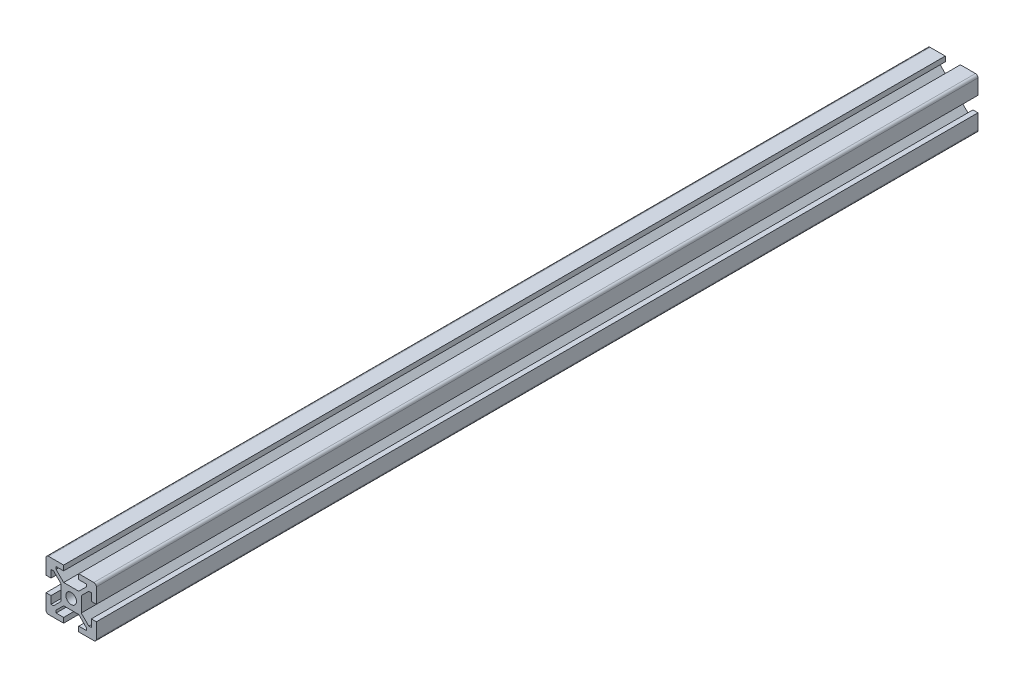
SolidWorks part; units mm, degrees
material "6063-O, Barra estrusa (SS)"
ref_plane "Piano frontale" through (0, 0, 0) normal (0, 0, 1) x (1, 0, 0)
ref_plane "Piano superiore" through (0, 0, 0) normal (0, 1, 0) x (1, 0, 0)
ref_plane "Piano destro" through (0, 0, 0) normal (1, 0, 0) x (0, 0, -1)
other "Lunghezza"
sketch "Schizzo1" plane through (0, 0, 0) normal (0, 0, 1) x (1, 0, 0)
  line L0 (-6, 8) -> (6, 8) construction
  line L1 (10, 3) -> (10, 10)
  line L2 (8, 3) -> (10, 3)
  line L3 (10, 10) -> (3, 10)
  line L4 (8, 6) -> (8, 3)
  line L5 (10, -10) -> (-10, 10) construction
  line L6 (10, 10) -> (-10, -10) construction
  line L7 (0, 23.5419) -> (0, -15.5419) construction
  line L8 (-13.4777, 0) -> (13.4408, 0) construction
  line L9 (-3, 4) -> (3, 4) construction
  line L10 (3, 4) -> (9, 10) construction
  line L11 (6, 11.4787) -> (6, 3.0667) construction
  line L12 (-6, 11.4787) -> (-6, 3.0667) construction
  line L13 (-3, 4) -> (-9, 10) construction
  line L14 (-3, 4) -> (-6, 7)
  line L15 (-6, 7) -> (-6, 8)
  line L16 (-6, 8) -> (-3, 8)
  line L17 (6, 8) -> (6, 7)
  line L18 (6, 7) -> (3, 4)
  line L19 (3, 4) -> (-3, 4)
  line L20 (-3, 8) -> (-3, 10)
  line L21 (6, 8) -> (3, 8)
  line L22 (3, 8) -> (3, 10)
  line L23 (-3, 10) -> (-10, 10)
  line L24 (7, 6) -> (8, 6)
  line L25 (4, 3) -> (7, 6)
  line L26 (4, -3) -> (4, 3)
  line L27 (7, -6) -> (4, -3)
  line L28 (8, -6) -> (7, -6)
  line L29 (8, -6) -> (8, -3)
  line L30 (8, -3) -> (10, -3)
  line L31 (10, -10) -> (10, -3)
  line L32 (3, -10) -> (10, -10)
  line L33 (3, -8) -> (3, -10)
  line L34 (6, -8) -> (3, -8)
  line L35 (6, -7) -> (6, -8)
  line L36 (3, -4) -> (6, -7)
  line L37 (-3, -4) -> (3, -4)
  line L38 (-6, -7) -> (-3, -4)
  line L39 (-6, -8) -> (-6, -7)
  line L40 (-6, -8) -> (-3, -8)
  line L41 (-3, -8) -> (-3, -10)
  line L42 (-10, -10) -> (-3, -10)
  line L43 (-10, -3) -> (-10, -10)
  line L44 (-8, -3) -> (-10, -3)
  line L45 (-8, -6) -> (-8, -3)
  line L46 (-7, -6) -> (-8, -6)
  line L47 (-4, -3) -> (-7, -6)
  line L48 (-4, 3) -> (-4, -3)
  line L49 (-7, 6) -> (-4, 3)
  line L50 (-8, 6) -> (-7, 6)
  line L51 (-8, 6) -> (-8, 3)
  line L52 (-8, 3) -> (-10, 3)
  line L53 (-10, 10) -> (-10, 3)
  circle A0 centre (0, 0) radius 2.1
  point P0 (0, 0)
  point P10 (0, 8)
  point P17 (0, 4)
  point P69 (0, 0)
  dimension "D6" = 4.2
  dimension "D1" = 20
  dimension "D2" = 10
  dimension "D3" = 2
  dimension "D4" = 12
  dimension "D5" = 4
  dimension "D7" = 4
  dimension "D8" = 6
  dimension "D9" = 6
  dimension "D10" = 3
  dimension "D11" = 4
extrude "Estrusione-Estrusione1" add sketch "Schizzo1" along normal blind 350
fillet "Raccordo1" radius 1 4 edges at (-10, -10, 175) (10, -10, 175) (-10, 10, 175) (10, 10, 175)
